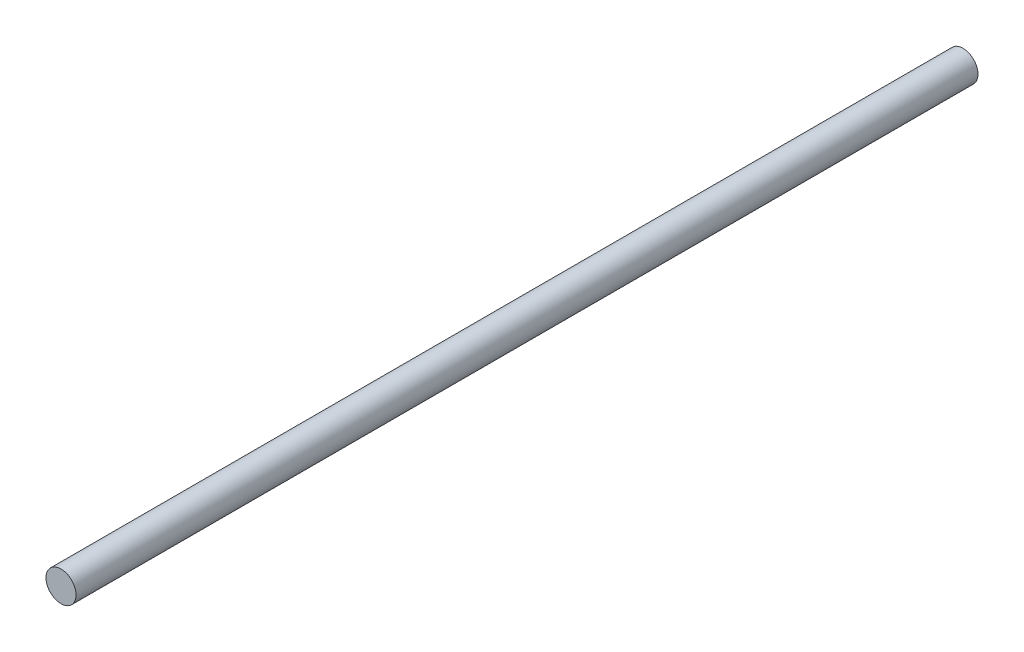
SolidWorks part; units mm, degrees
material "AISI 304"
ref_plane "Front Plane" through (0, 0, 0) normal (0, 0, 1) x (1, 0, 0)
ref_plane "Top Plane" through (0, 0, 0) normal (0, 1, 0) x (1, 0, 0)
ref_plane "Right Plane" through (0, 0, 0) normal (1, 0, 0) x (0, 0, -1)
sketch "Sketch1" plane through (0, 0, 0) normal (0, 0, 1) x (1, 0, 0)
  circle A0 centre (0, 0) radius 2.5
  dimension "D1" = 5
extrude "Boss-Extrude1" add sketch "Sketch1" along normal blind 150 contours A0
